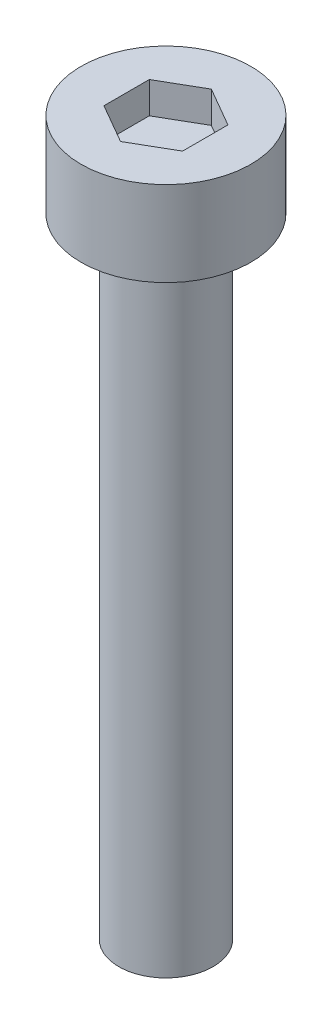
SolidWorks part; units mm, degrees
ref_plane "Front Plane" through (0, 0, 0) normal (0, 0, 1) x (1, 0, 0)
ref_plane "Top Plane" through (0, 0, 0) normal (0, 1, 0) x (1, 0, 0)
ref_plane "Right Plane" through (0, 0, 0) normal (1, 0, 0) x (0, 0, -1)
sketch "Sketch1" plane through (0, 0, 0) normal (0, 1, 0) x (1, 0, 0)
  circle A0 centre (0, 0) radius 2.7
extrude "Boss-Extrude1" add sketch "Sketch1" along normal blind 2.7
sketch "Sketch2" plane through (0, 2.7, 0) normal (0, 1, 0) x (1, 0, 0)
  line L1 (0, 1.4434) -> (-1.25, 0.7217)
  line L2 (-1.25, 0.7217) -> (-1.25, -0.7217)
  line L3 (-1.25, -0.7217) -> (0, -1.4434)
  line L4 (0, -1.4434) -> (1.25, -0.7217)
  line L5 (1.25, -0.7217) -> (1.25, 0.7217)
  line L6 (1.25, 0.7217) -> (0, 1.4434)
  circle A0 centre (0, 0) radius 1.25 construction
extrude "Cut-Extrude1" cut sketch "Sketch2" against normal blind 1
sketch "Sketch3" plane through (0, 0, 0) normal (0, -1, 0) x (1, 0, 0)
  circle A0 centre (0, 0) radius 1.5
extrude "Boss-Extrude2" add sketch "Sketch3" along normal blind 20
